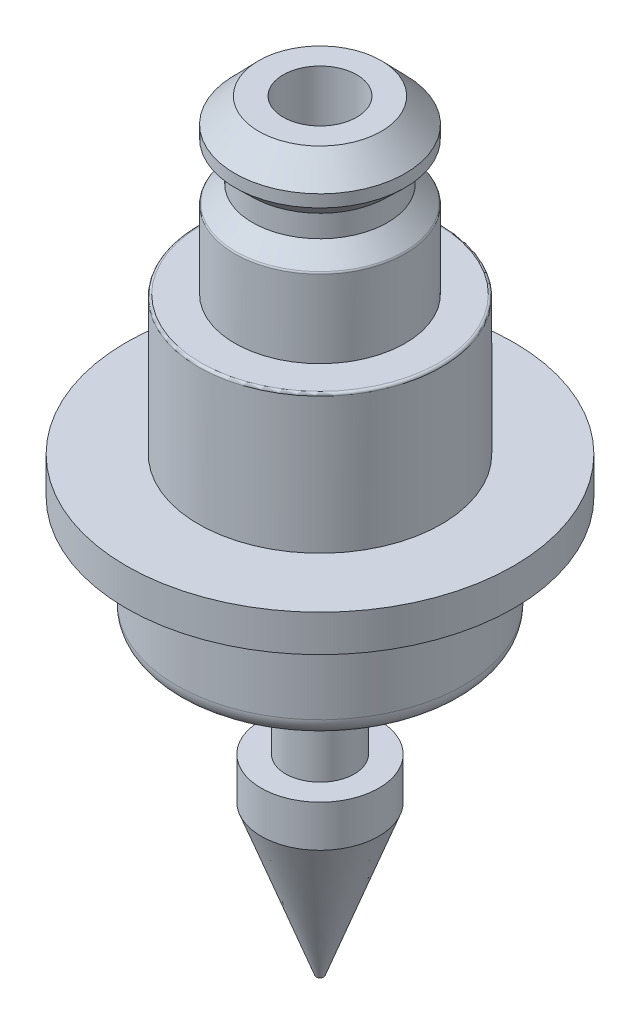
SolidWorks part; units mm, degrees
ref_plane "Front" through (0, 0, 0) normal (0, 0, 1) x (1, 0, 0)
ref_plane "Top" through (0, 0, 0) normal (0, 1, 0) x (1, 0, 0)
ref_plane "Right" through (0, 0, 0) normal (1, 0, 0) x (0, 0, -1)
sketch "Sketch1" plane through (0, 0, 0) normal (0, 0, 1) x (1, 0, 0)
  line L0 (0, 0) -> (0, 14.15) construction
  line L1 (0, 14.15) -> (1.5, 14.15) construction
  line L2 (1.5, 14.15) -> (1.5, 0) construction
  line L3 (1.5, 0) -> (0, 0) construction
  line L4 (1.5, 14.15) -> (2.5, 14.15)
  line L5 (2.5, 14.15) -> (3.475, 13.15)
  line L6 (3.475, 13.15) -> (3.475, 12.65)
  line L7 (3.475, 12.65) -> (2.75, 11.95)
  line L8 (2.75, 11.95) -> (2.75, 11.05)
  line L9 (2.75, 11.05) -> (3.475, 10.35)
  line L10 (3.475, 10.35) -> (3.475, 7.15)
  line L11 (3.475, 7.15) -> (4.955, 7.15)
  line L12 (4.955, 7.15) -> (4.955, 1.5)
  line L13 (4.955, 1.5) -> (7.9, 1.5)
  line L14 (7.9, 1.5) -> (7.9, 0)
  line L15 (7.9, 0) -> (5.85, 0)
  line L16 (5.85, 0) -> (5.85, -4.5)
  line L17 (5.85, -4.5) -> (1.4, -4.5)
  line L18 (3.475, 12.65) -> (3.475, 10.35) construction
  line L19 (2.75, 11.5) -> (3.475, 11.5) construction
  line L20 (1.4, -4.5) -> (1.4, -9.1)
  line L21 (1.4, -9.1) -> (2.4, -9.1)
  line L22 (2.4, -9.1) -> (2.4, -10.8)
  line L23 (2.4, -10.8) -> (0.15, -16.9)
  line L24 (0.15, -16.9) -> (0.15, 0)
  line L25 (0.15, 0) -> (1.5, 0)
  line L26 (1.5, 0) -> (1.5, 14.15)
  dimension "D1" = 5
  dimension "D2" = 6.95
  dimension "D3" = 3
  dimension "D4" = 5.5
  dimension "D5" = 12.65
  dimension "D6" = 15.8
  dimension "D7" = 11.7
  dimension "D8" = 4.5
  dimension "D9" = 1.5
  dimension "D10" = 9.91
  dimension "D11" = 7
  dimension "D12" = 1
  dimension "D13" = 1.5
  dimension "D14" = 3.8
  dimension "D15" = 2.2
  dimension "D16" = 0.3
  dimension "D17" = 2.8
  dimension "D18" = 4.8
  dimension "D19" = 1.7
  dimension "D20" = 7.8
  dimension "D21" = 12.4
revolve "Revolve1" add sketch "Sketch1" angle 360 about L0
fillet "Fillet1" radius 0.75 1 edges at (0, -4.5, -5.85)
fillet "Fillet2" radius 0.1 2 edges at (0, 10.35, -3.475) (0, 7.15, -4.955)
